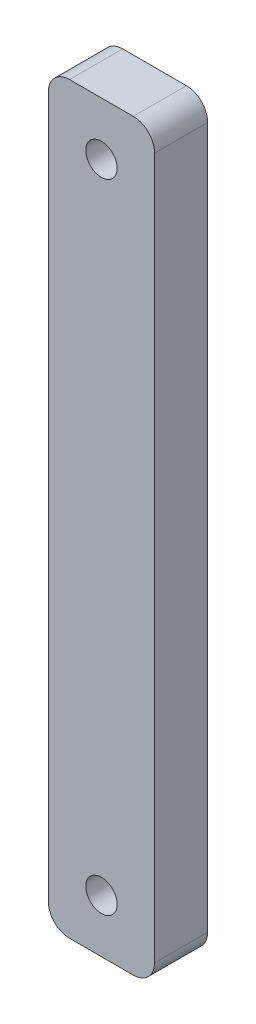
SolidWorks part; units mm, degrees
ref_plane "Front Plane" through (0, 0, 0) normal (0, 0, 1) x (1, 0, 0)
ref_plane "Top Plane" through (0, 0, 0) normal (0, 1, 0) x (1, 0, 0)
ref_plane "Right Plane" through (0, 0, 0) normal (1, 0, 0) x (0, 0, -1)
sketch "Sketch1" plane through (0, 0, 0) normal (0, 0, 1) x (1, 0, 0)
  line L1 (-5, 35) -> (5, 35)
  line L2 (-5, 35) -> (-5, -35)
  line L3 (-5, -35) -> (5, -35)
  line L4 (5, 35) -> (5, -35)
  line L5 (0, -35) -> (0, 35) construction
  line L6 (-5, 0) -> (5, 0) construction
  circle A0 centre (0, 30) radius 1.475
  circle A1 centre (0, -30) radius 1.475
  point P0 (0, 0)
  dimension "D3" = 2.95
  dimension "D1" = 70
  dimension "D2" = 10
  dimension "D4" = 30
extrude "Boss-Extrude1" add sketch "Sketch1" along normal blind 5
fillet "Fillet1" radius 2 4 edges at (5, -35, 2.5) (-5, -35, 2.5) (-5, 35, 2.5) (5, 35, 2.5)
